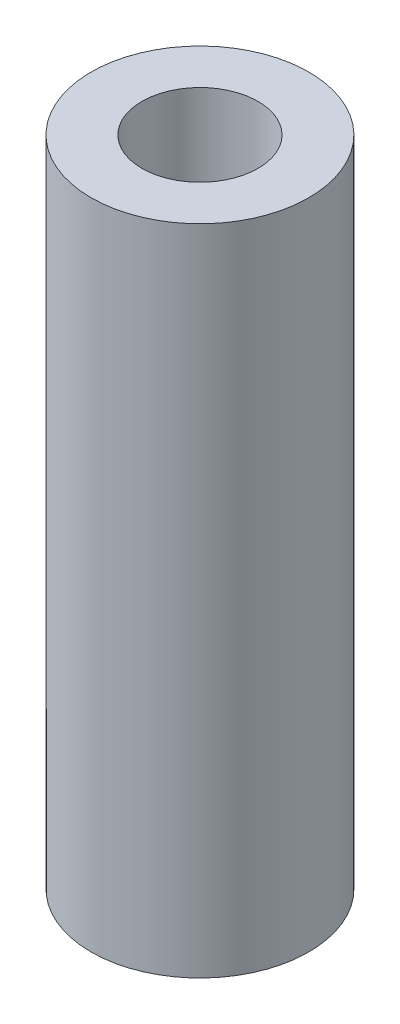
SolidWorks part; units mm, degrees
ref_plane "Front" through (0, 0, 0) normal (0, 0, 1) x (1, 0, 0)
ref_plane "Top" through (0, 0, 0) normal (0, 1, 0) x (1, 0, 0)
ref_plane "Right" through (0, 0, 0) normal (1, 0, 0) x (0, 0, -1)
sketch "Sketch1" plane through (0, 0, 0) normal (0, 1, 0) x (1, 0, 0)
  circle A0 centre (0, 0) radius 3
  circle A1 centre (0, 0) radius 1.6
  dimension "D1" = 3.2
  dimension "D2" = 6
extrude "Boss-Extrude1" add sketch "Sketch1" along normal blind 18
